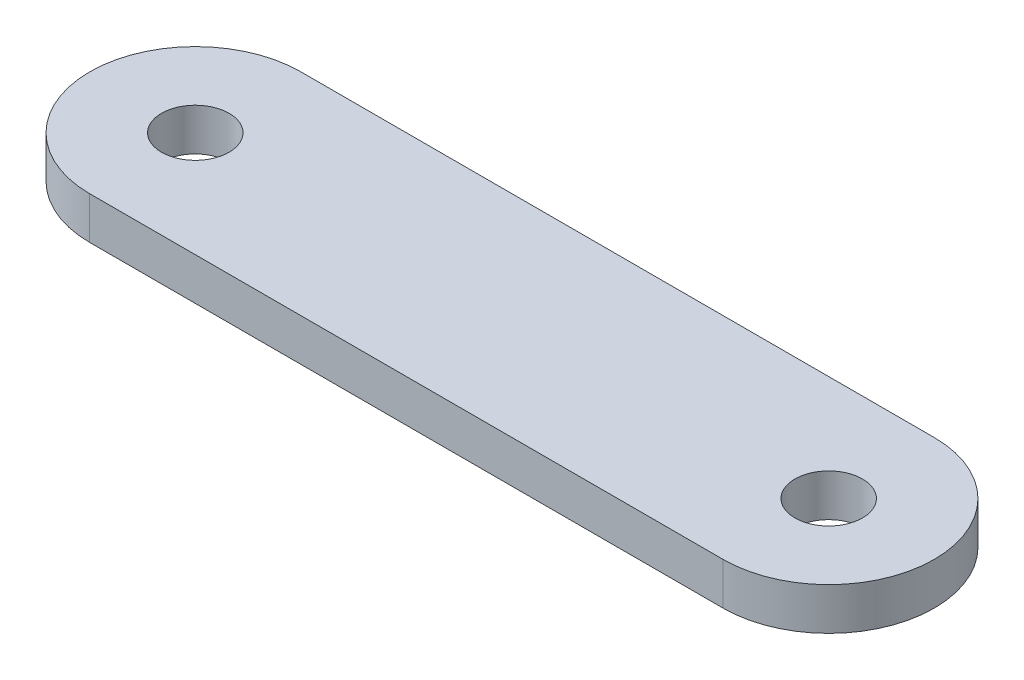
SolidWorks part; units mm, degrees
material "Thornel Mat VMA"
ref_plane "前视基准面" through (0, 0, 0) normal (0, 0, 1) x (1, 0, 0)
ref_plane "上视基准面" through (0, 0, 0) normal (0, 1, 0) x (1, 0, 0)
ref_plane "右视基准面" through (0, 0, 0) normal (1, 0, 0) x (0, 0, -1)
sketch "草图1" plane through (0, 0, 0) normal (0, 1, 0) x (1, 0, 0)
  line L0 (0, 0) -> (-30, 0) construction
  line L1 (-30, 0) -> (0, 0) construction
  line L2 (-30, 5) -> (0, 5)
  line L3 (-30, -5) -> (0, -5)
  arc A0 (-30, 5) -> (-30, -5) centre (-30, 0) ccw
  arc A1 (0, -5) -> (0, 5) centre (0, 0) ccw
  circle A2 centre (-30, 0) radius 1.6
  circle A3 centre (0, 0) radius 1.6
  point P3 (-15, 0)
  dimension "D2" = 3.2
  dimension "D3" = 3.2
  dimension "D1" = 30
extrude "凸台-拉伸1" add sketch "草图1" along normal blind 2
